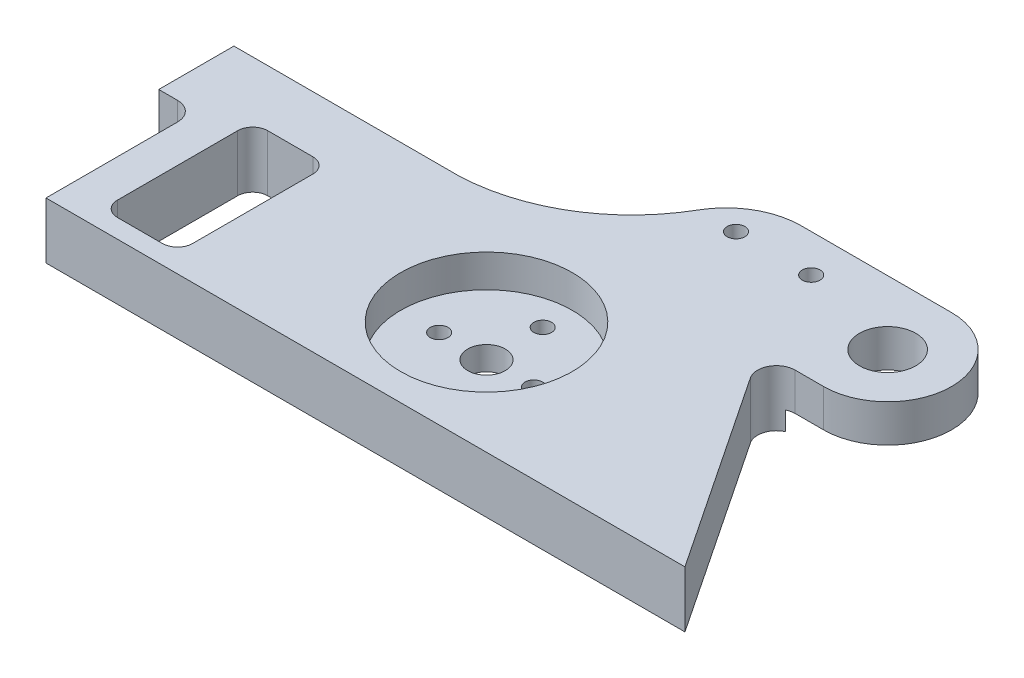
SolidWorks part; units mm, degrees
material "UHMW"
ref_plane "Front Plane" through (0, 0, 0) normal (0, 0, 1) x (1, 0, 0)
ref_plane "Top Plane" through (0, 0, 0) normal (0, 1, 0) x (1, 0, 0)
ref_plane "Right Plane" through (0, 0, 0) normal (1, 0, 0) x (0, 0, -1)
other "Bounding Box"
ref_plane "Default Plane" through (-8.9266, -12.7485, 0) normal (-0.1736, 0.9848, 0) x (0.9848, 0.1736, 0)
sketch "Sketch1" plane through (0, 0, 0) normal (0, 1, 0) x (1, 0, 0)
  line L0 (0, 0) -> (38.1, 0)
  line L1 (88.9, 0) -> (114.3, -38.1)
  line L2 (114.3, -38.1) -> (6.35, -38.1)
  line L3 (6.35, -38.1) -> (6.35, -12.7)
  line L4 (6.35, -12.7) -> (0, -12.7)
  line L5 (0, -12.7) -> (0, 0)
  line L6 (99.6289, 0) -> (88.9, 0)
  line L9 (99.6289, 21.632) -> (74.2289, 21.632)
  line L10 (61.7205, -19.05) -> (99.6289, 10.816) construction
  circle A0 centre (99.6289, 10.816) radius 4.7625
  arc A1 (99.6289, 21.632) -> (99.6289, 0) centre (99.6289, 10.816) cw
  arc A4 (74.2289, 21.632) -> (63.2185, 15.2614) centre (74.2289, 8.932) ccw
  arc A5 (63.2185, 15.2614) -> (38.1, 0) centre (36.7936, 30.452) cw
  circle A6 centre (69.5685, 15.2614) radius 1.5
  circle A7 centre (82.2685, 15.2614) radius 1.5
  circle B0 centre (69.7205, -19.05) radius 1.5
  circle B1 centre (61.7205, -28.55) radius 1.5
  circle B2 centre (53.7205, -19.05) radius 1.5
  circle B3 centre (61.7205, -9.55) radius 1.5
  circle B4 centre (61.7205, -19.05) radius 3.175
  dimension "D7" = 50.8
  dimension "D8" = 9.525
  dimension "D9" = 10.7289
  dimension "D6" = 10.816
  dimension "D10" = 30.48
  dimension "D16" = 12.7
  dimension "D19" = 3
  dimension "D1" = 6.35
  dimension "D2" = 38.1
  dimension "D3" = 107.95
  dimension "D4" = 88.9
  dimension "D5" = 12.7
  dimension "D11" = 48.26
  dimension "D12" = 19.05
  dimension "D17" = 38.1
  dimension "D18" = 25.4
  dimension "D20" = 6.35
  dimension "D21" = 12.7
sketch_block_instance "Block1-1"
sketch_block "Block1" parameters "D1"=6.35
extrude "Boss-Extrude1" add sketch "Sketch1" along normal blind 9.525
fillet "Fillet1" radius 3.175 1 edges at (88.9, 4.7625, 0)
fillet "Fillet2" radius 3.175 1 edges at (6.35, 4.7625, 12.7)
sketch "Sketch2" plane through (0, 9.525, 0) normal (0, 1, 0) x (1, 0, 0)
  circle A0 centre (61.7205, -19.05) radius 14.5
  dimension "D1" = 29
extrude "Cut-Extrude1" cut sketch "Sketch2" against normal blind 5.525
sketch "Sketch3" plane through (0, 0, 0) normal (0, 1, 0) x (1, 0, 0)
  circle A4 centre (99.6289, 10.816) radius 12.7
  dimension "D1" = 25.4
extrude "Cut-Extrude2" cut sketch "Sketch3" along normal blind 3.175
sketch "Sketch4" plane through (0, 0, 0) normal (0, -1, 0) x (1, 0, 0)
  line L0 (12.7, 34.925) -> (12.7, 9.525)
  line L1 (12.7, 9.525) -> (25.4, 9.525)
  line L2 (25.4, 9.525) -> (25.4, 34.925)
  line L3 (25.4, 34.925) -> (12.7, 34.925)
  line L4 (6.35, 15.875) -> (6.35, 38.1) construction
  line L5 (6.35, 38.1) -> (114.3, 38.1) construction
  dimension "D1" = 25.4
  dimension "D2" = 12.7
  dimension "D3" = 6.35
  dimension "D4" = 3.175
extrude "Cut-Extrude3" cut sketch "Sketch4" against normal through all
fillet "Fillet3" radius 2.54 4 edges at (25.4, 4.7625, 34.925) (12.7, 4.7625, 9.525) (25.4, 4.7625, 9.525) (12.7, 4.7625, 34.925)
